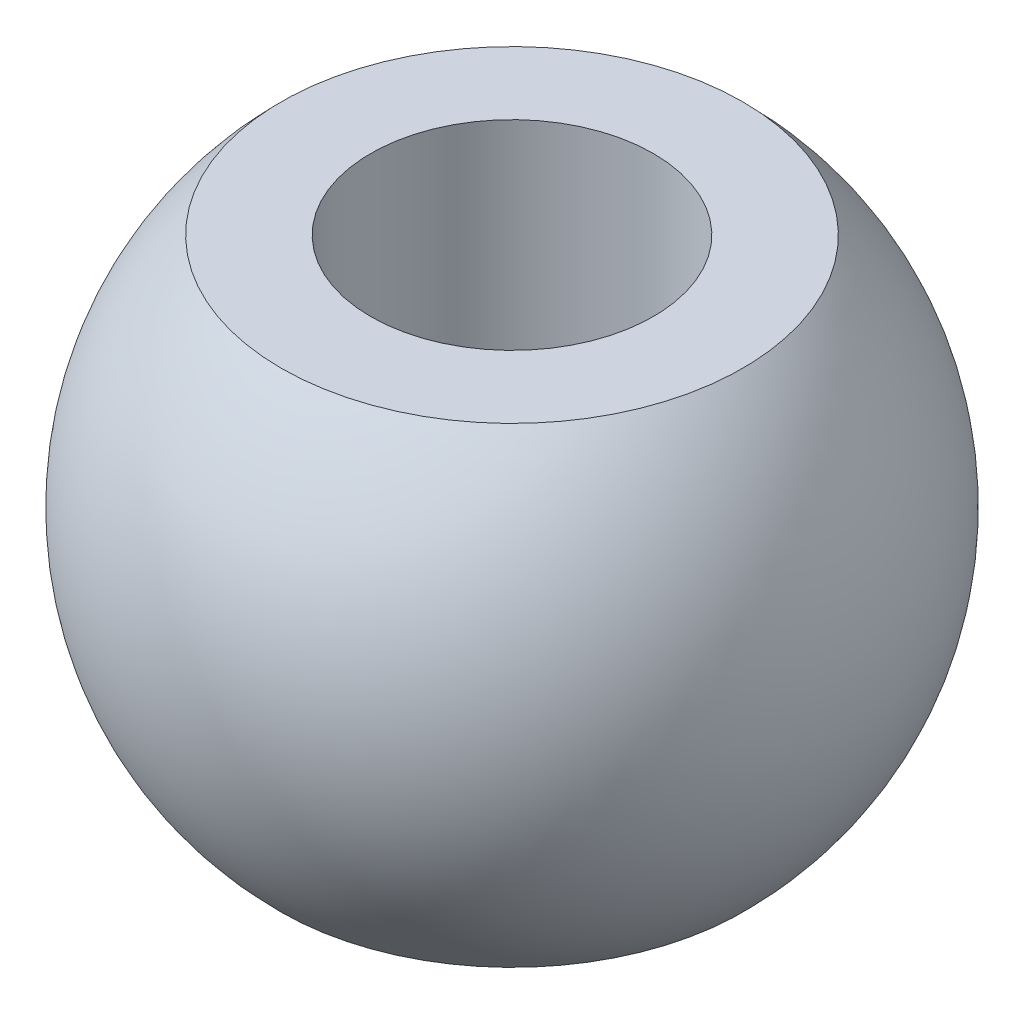
SolidWorks part; units mm, degrees
ref_plane "Front Plane" through (0, 0, 0) normal (0, 0, 1) x (1, 0, 0)
ref_plane "Top Plane" through (0, 0, 0) normal (0, 1, 0) x (1, 0, 0)
ref_plane "Right Plane" through (0, 0, 0) normal (1, 0, 0) x (0, 0, -1)
sketch "Sketch1" plane through (0, 0, 0) normal (0, 0, 1) x (1, 0, 0)
  line L0 (0, 3.2463) -> (0, -3.291) construction
  line L1 (-1.5, 2.5) -> (-1.5, -2.5)
  line L2 (-1.5, 2.5) -> (-2.4495, 2.5)
  line L3 (-1.5, -2.5) -> (-2.4495, -2.5)
  circle A0 centre (0, 0) radius 3.5 construction
  arc A1 (-2.4495, -2.5) -> (-2.4495, 2.5) centre (0, 0) cw
  circle A2 centre (0, 0) radius 4 construction
  point P5 (-1.5, 0)
  dimension "D3" = 7
  dimension "D4" = 0.5
  dimension "D1" = 5
  dimension "D2" = 1.5
revolve "Revolve1" add sketch "Sketch1" angle 360 about L0
